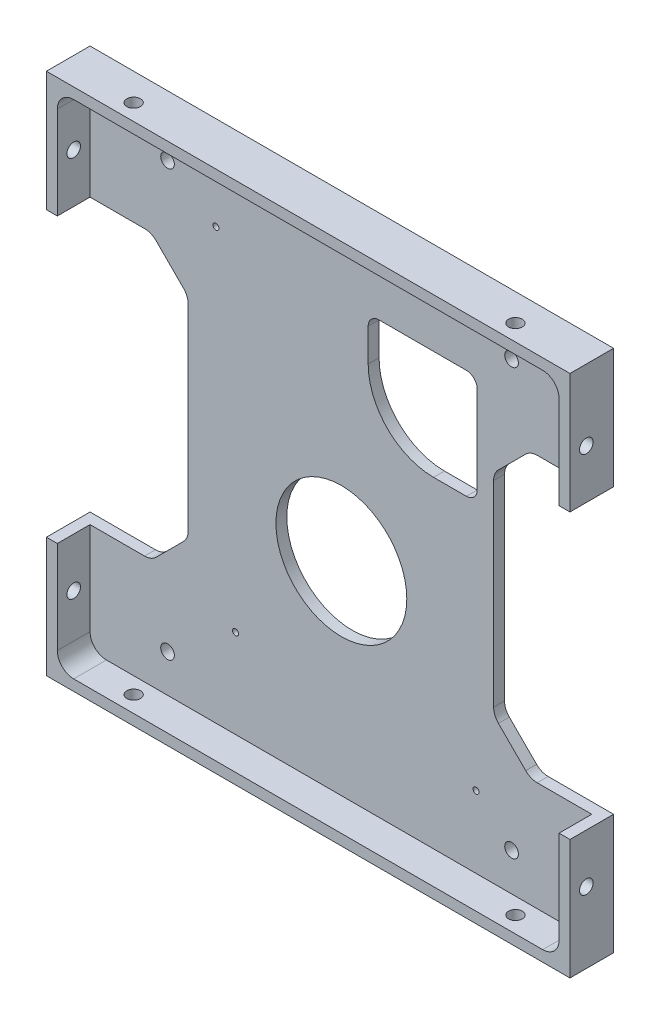
SolidWorks part; units mm, degrees
material "6061-T6 (SS)"
ref_plane "Front" through (0, 0, 0) normal (0, 0, 1) x (1, 0, 0)
ref_plane "Top" through (0, 0, 0) normal (0, 1, 0) x (1, 0, 0)
ref_plane "Right" through (0, 0, 0) normal (1, 0, 0) x (0, 0, -1)
sketch "Sketch1" plane through (0, 0, 0) normal (0, 0, 1) x (1, 0, 0)
  line L1 (-48, -48) -> (48, -48)
  line L2 (-48, -48) -> (-48, 48)
  line L3 (-48, 48) -> (48, 48)
  line L4 (48, -48) -> (48, 48)
  line L5 (-48, -48) -> (48, 48) construction
  line L6 (-48, 48) -> (48, -48) construction
  point P0 (0, 0)
  dimension "D1" = 96
  dimension "D2" = 96
extrude "Boss-Extrude1" add sketch "Sketch1" along normal blind 8
sketch "Sketch2" plane through (0, 0, 8) normal (0, 0, 1) x (1, 0, 0)
  line L1 (46, -46) -> (-46, -46)
  line L2 (46, -46) -> (46, 46)
  line L3 (46, 46) -> (-46, 46)
  line L4 (-46, -46) -> (-46, 46)
  line L5 (46, -46) -> (-46, 46) construction
  line L6 (46, 46) -> (-46, -46) construction
  point P0 (0, 0)
  dimension "D1" = 92
  dimension "D2" = 92
extrude "Component Platform" cut sketch "Sketch2" against normal blind 6
sketch "Sketch3" plane through (0, 0, 2) normal (0, 0, 1) x (1, 0, 0)
  line L1 (-33.8787, -25.1213) -> (-28.8787, -20.1213)
  line L2 (-33.8787, 25.1213) -> (-28.8787, 20.1213)
  line L3 (-28, -18) -> (-28, 18)
  line L4 (-48, -26) -> (-36, -26)
  line L7 (-48, 48) -> (-48, -48) construction
  line L8 (0, -56.7987) -> (0, 73.4321) construction
  line L9 (46, -46) -> (-57.8147, 57.8147) construction
  line L18 (46, 46) -> (-68.5705, -68.5705) construction
  line L23 (-48, 26) -> (-36, 26)
  line L26 (-48, -26) -> (-48, 26)
  line L28 (-48, -48) -> (48, -48) construction
  line L29 (48, -26) -> (48, 26)
  line L30 (48, 26) -> (36, 26)
  line L31 (33.8787, 25.1213) -> (28.8787, 20.1213)
  line L32 (28, -18) -> (28, 18)
  line L33 (33.8787, -25.1213) -> (28.8787, -20.1213)
  line L34 (48, -26) -> (36, -26)
  arc A3 (-28.8787, -20.1213) -> (-28, -18) centre (-31, -18) ccw
  arc A4 (-28.8787, 20.1213) -> (-28, 18) centre (-31, 18) cw
  arc A13 (-33.8787, -25.1213) -> (-36, -26) centre (-36, -23) cw
  arc A15 (-33.8787, 25.1213) -> (-36, 26) centre (-36, 23) ccw
  arc A17 (33.8787, 25.1213) -> (36, 26) centre (36, 23) cw
  arc A18 (28.8787, 20.1213) -> (28, 18) centre (31, 18) ccw
  arc A19 (28.8787, -20.1213) -> (28, -18) centre (31, -18) cw
  arc A20 (33.8787, -25.1213) -> (36, -26) centre (36, -23) ccw
  point P0 (-48, 0)
  point P37 (-48, 0)
  dimension "D2" = 3
  dimension "D3" = 3
  dimension "D4" = 20
  dimension "D6" = 3
  dimension "D7" = 3
  dimension "D8" = 135
  dimension "D5" = 52
  dimension "D9" = 135
  dimension "D10" = 12
  dimension "D11" = 12
  dimension "D12" = 48
extrude "Cable Slots" cut sketch "Sketch3" against normal mid plane 12
ref_plane "Center Y-Plane" through (0, 0, 0) normal (1, 0, 0) x (0, 0, -1)
ref_plane "Center X-Plane" through (0, 0, 0) normal (0, -1, 0) x (-1, 0, 0)
fillet "Inner Corner Fillets" radius 3 4 edges at (46, -46, 5) (-46, -46, 5) (46, 46, 5) (-46, 46, 5)
sketch "Sketch7" plane through (0, 0, 2) normal (0, 0, 1) x (1, 0, 0)
  line L0 (-48, -48) -> (48, -48) construction
  line L4 (48, -48) -> (48, -26) construction
  line L5 (48, 26) -> (48, 48) construction
  line L7 (48, 48) -> (-48, 48) construction
  line L8 (-43, -46) -> (43, -46) construction
  point P1 (-19.32, -29.75)
  point P4 (24.78, -32.85)
  point P5 (24.78, 32.85)
  point P8 (-22.92, 32.85)
  point P12 (24.7, -56.85)
  point P13 (24.7, 48)
  point P14 (-19.4, -48)
  point P15 (48, -32.85)
  point P16 (-48, -32.85)
  point P18 (-19.4, 48)
  point P19 (48, -32.85)
  point P20 (-48, -32.85)
  point P24 (48, 43.7)
  point P25 (-48.7506, 43.7)
  point P27 (48, 32.85)
  point P28 (-23, -48)
  point P29 (-23, 48)
  point P31 (-48.7506, 32.85)
  dimension "D1" = 16.25
  dimension "D2" = 47.7
  dimension "D3" = 15.15
  dimension "D4" = 23.22
  dimension "D5" = 23.22
  dimension "D6" = 44.1
  dimension "D7" = 15.15
  dimension "D8" = 15.15
sketch "Sketch9" plane through (0, 0, 2) normal (0, 0, 1) x (1, 0, 0)
  line L0 (25, 31) -> (25, 15)
  line L1 (23, 33) -> (7, 33)
  line L3 (23, 13) -> (17, 13)
  line L4 (5, 25) -> (5, 31)
  line L6 (48, 26) -> (48, 48) construction
  line L8 (48, 48) -> (-48, 48) construction
  arc A0 (5, 25) -> (17, 13) centre (17, 25) ccw
  arc A1 (25, 15) -> (23, 13) centre (23, 15) cw
  arc A2 (25, 31) -> (23, 33) centre (23, 31) ccw
  arc A3 (7, 33) -> (5, 31) centre (7, 31) ccw
  point P11 (25, 13)
  point P15 (25, 33)
  point P18 (5, 33)
  dimension "D1" = 12
  dimension "D6" = 2
  dimension "D2" = 20
  dimension "D3" = 20
  dimension "D4" = 15
  dimension "D5" = 23
sketch "Sketch11" plane through (48, 0, 0) normal (1, 0, 0) x (0, 0, -1)
  line L0 (-5, -48) -> (-5, 48) construction
  line L1 (-8, -48) -> (0, -48) construction
  line L2 (-8, 48) -> (0, 48) construction
  line L3 (-8, -48) -> (-8, -26) construction
  dimension "D1" = 3
sketch "Sketch12" plane through (0, 48, 0) normal (0, 1, 0) x (1, 0, 0)
  line L0 (-48, -5) -> (48, -5) construction
  line L1 (-48, -8) -> (-48, 0) construction
  line L2 (48, -8) -> (48, 0) construction
  line L3 (48, -8) -> (-48, -8) construction
  dimension "D1" = 3
hole_wizard "M3x0.5 Tapped Hole1" positions "Sketch13" profile "Sketch14" tap size "M3x0.5" standard "ANSI Metric"
sketch "Sketch13" plane through (48, 0, 0) normal (1, 0, 0) x (0, 0, -1)
  line L0 (-5, -48) -> (-5, 48) construction
  point P0 (-5, -35)
  point P4 (-5, 35)
  dimension "D1" = 70
  dimension "D2" = 35
sketch "Sketch14" plane through (48, -35, 5) normal (0, 1, 0) x (0, 0, -1)
  line L0 (0, 0) -> (0, 10.7511)
  line L1 (0, 10.7511) -> (1.25, 10)
  line L2 (1.25, 10) -> (1.25, 0)
  line L5 (1.25, 0) -> (0, 0)
  line L10 (0, 10.7511) -> (-1.25, 10) construction
  line L11 (0, -6.35) -> (0, 107.95) construction
  dimension "Tap Drill Dia." = 2.5
  dimension "Tap Drill Depth" = 10
  dimension "Drill Angle" = 118
hole_wizard "M3x0.5 Tapped Hole2" positions "Sketch15" profile "Sketch16" tap size "M3x0.5" standard "ANSI Metric"
sketch "Sketch15" plane through (0, 48, 0) normal (0, 1, 0) x (1, 0, 0)
  line L0 (-48, -5) -> (48, -5) construction
  point P0 (35, -5)
  point P4 (-35, -5)
  dimension "D1" = 70
  dimension "D2" = 35
sketch "Sketch16" plane through (35, 48, 5) normal (1, 0, 0) x (0, 0, 1)
  line L0 (0, 0) -> (0, 10.7511)
  line L1 (0, 10.7511) -> (1.25, 10)
  line L2 (1.25, 10) -> (1.25, 0)
  line L5 (1.25, 0) -> (0, 0)
  line L10 (0, 10.7511) -> (-1.25, 10) construction
  line L11 (0, -6.35) -> (0, 107.95) construction
  dimension "Tap Drill Dia." = 2.5
  dimension "Tap Drill Depth" = 10
  dimension "Drill Angle" = 118
mirror "Mirror1" about plane through (0, 0, 0) normal (1, 0, 0) of "M3x0.5 Tapped Hole1"
mirror "Mirror2" about plane through (0, 0, 0) normal (0, -1, 0) of "M3x0.5 Tapped Hole2"
sketch "Sketch22" plane through (0, 0, 2) normal (0, 0, 1) x (1, 0, 0)
  line L2 (46, -43) -> (46, -26) construction
  line L3 (-43, -46) -> (43, -46) construction
  line L4 (-46, -26) -> (-46, -43) construction
  line L6 (46, 26) -> (46, 43) construction
  line L7 (43, 46) -> (-43, 46) construction
  line L8 (-46, 43) -> (-46, 26) construction
  point P0 (-31.791, -39.06)
  point P1 (-31.791, 38.94)
  point P2 (31.29, 38.94)
  point P3 (31.29, -39.06)
  dimension "D1" = 14.71
  dimension "D2" = 6.94
  dimension "D3" = 6.94
  dimension "D4" = 14.209
  dimension "D5" = 14.71
  dimension "D6" = 7.06
  dimension "D7" = 7.06
  dimension "D8" = 14.209
hole_wizard "M1.4x0.3 Tapped Hole1" positions "Sketch27" profile "Sketch28" tap size "M1.4x0.3" standard "ANSI Metric"
sketch "Sketch27" plane through (0, 0, 2) normal (0, 0, 1) x (1, 0, 0)
  point P0 (-19.32, -29.75)
  point P3 (24.78, -32.85)
  point P9 (-22.92, 32.85)
  point P12 (0, 0)
sketch "Sketch28" plane through (-19.32, -29.75, 2) normal (1, 0, 0) x (0, -1, 0)
  line L0 (0, 0) -> (0, 4.0305)
  line L1 (0, 4.0305) -> (0.55, 3.7)
  line L2 (0.55, 3.7) -> (0.55, 0)
  line L5 (0.55, 0) -> (0, 0)
  line L10 (0, 4.0305) -> (-0.55, 3.7) construction
  line L11 (0, -6.35) -> (0, 107.95) construction
  dimension "Tap Drill Dia." = 1.1
  dimension "Tap Drill Depth" = 3.7
  dimension "Drill Angle" = 118
sketch "Sketch29" plane through (0, 0, 0) normal (0, 0, -1) x (-1, 0, 0)
  line L0 (28, 18) -> (28, -18) construction
  line L2 (48, -48) -> (-48, -48) construction
  circle A0 centre (-0.0819, -8.7479) radius 12
  dimension "D1" = 24
  dimension "D2" = 28.0819
  dimension "D3" = 39.2521
extrude "HDD Extrusion Cutout" cut sketch "Sketch29" against normal blind 10
extrude "HDD Extrusion Cutout 2" cut sketch "Sketch9" against normal blind 10
hole_wizard "M3x0.5 Tapped Hole3" positions "Sketch30" profile "Sketch31" tap size "M3x0.5" standard "ANSI Metric"
sketch "Sketch30" plane through (0, 0, 2) normal (0, 0, 1) x (1, 0, 0)
  point P0 (-31.791, -39.06)
  point P3 (31.29, -39.06)
  point P6 (31.29, 38.94)
  point P9 (-31.791, 38.94)
sketch "Sketch31" plane through (-31.791, -39.06, 2) normal (1, 0, 0) x (0, -1, 0)
  line L0 (0, 0) -> (0, 10.7511)
  line L1 (0, 10.7511) -> (1.25, 10)
  line L2 (1.25, 10) -> (1.25, 0)
  line L5 (1.25, 0) -> (0, 0)
  line L10 (0, 10.7511) -> (-1.25, 10) construction
  line L11 (0, -6.35) -> (0, 107.95) construction
  dimension "Tap Drill Dia." = 2.5
  dimension "Tap Drill Depth" = 10
  dimension "Drill Angle" = 118
